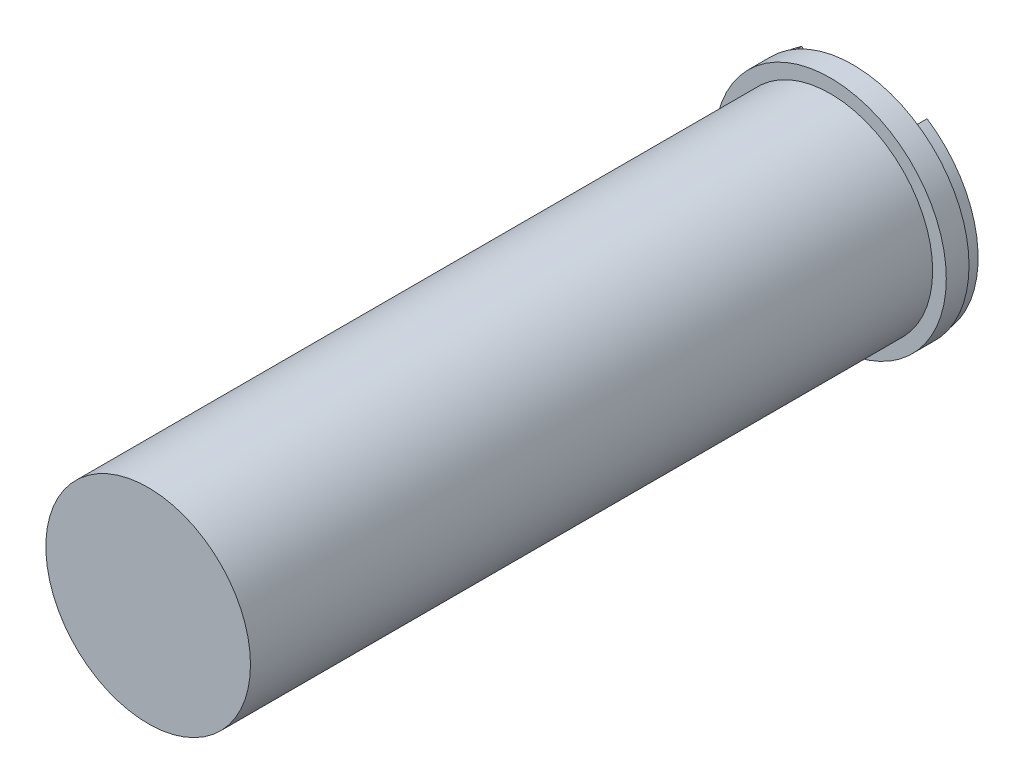
SolidWorks part; units mm, degrees
ref_plane "Спереди" through (0, 0, 0) normal (0, 0, 1) x (1, 0, 0)
ref_plane "Сверху" through (0, 0, 0) normal (0, 1, 0) x (1, 0, 0)
ref_plane "Справа" through (0, 0, 0) normal (1, 0, 0) x (0, 0, -1)
sketch "Эскиз1" plane through (0, 0, 0) normal (0, 0, 1) x (1, 0, 0)
  circle A0 centre (0, 0) radius 5.1
  dimension "D1" = 10.2
extrude "Бобышка-Вытянуть1" add sketch "Эскиз1" along normal blind 1
sketch "Эскиз2" plane through (0, 0, 1) normal (0, 0, 1) x (1, 0, 0)
  circle A0 centre (0, 0) radius 4.5
  dimension "D1" = 9
extrude "Бобышка-Вытянуть2" add sketch "Эскиз2" along normal blind 30
sketch "Эскиз4" plane through (0, 0, 0) normal (0, 0, -1) x (-1, 0, 0)
  line L0 (0, 4) -> (0, -4) construction
  line L1 (-3.9686, 0.5) -> (-0.5, 0.5)
  line L3 (-3.9686, -0.5) -> (3.9686, -0.5)
  line L5 (0.5, 0.5) -> (3.9686, 0.5)
  line L8 (2.757, 4.1712) -> (0, 1.4142)
  line L10 (2.8284, 2.8284) -> (0.5, 0.5)
  line L13 (-2.8284, 2.8284) -> (-0.5, 0.5)
  line L14 (-2.757, 4.1712) -> (0, 1.4142)
  arc A0 (-2.757, 4.1712) -> (2.757, 4.1712) centre (0, 0) ccw
  arc A1 (-3.9686, -0.5) -> (3.9686, -0.5) centre (0, 0) ccw
  arc A2 (-2.8284, 2.8284) -> (-3.9686, 0.5) centre (0, 0) ccw
  arc A3 (3.9686, 0.5) -> (2.8284, 2.8284) centre (0, 0) ccw
  dimension "D1" = 10
  dimension "D2" = 8
  dimension "D3" = 1
  dimension "D4" = 1
  dimension "D5" = 45
  dimension "D6" = 45
  dimension "D7" = 1
  dimension "D8" = 0.5
  dimension "D9" = 0.5
extrude "Бобышка-Вытянуть3" add sketch "Эскиз4" along normal blind 0.5 separate body
